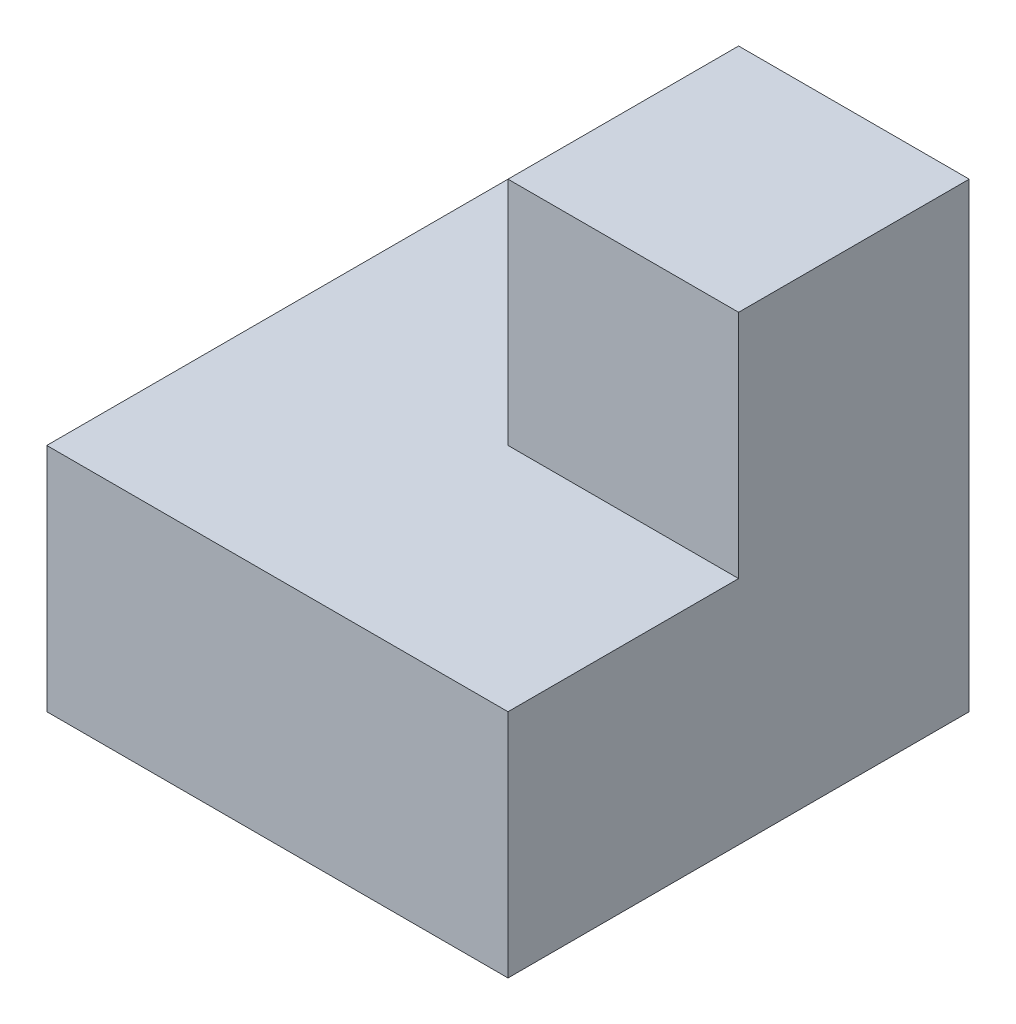
SolidWorks part; units mm, degrees
ref_plane "Front" through (0, 0, 0) normal (0, 0, 1) x (1, 0, 0)
ref_plane "Top" through (0, 0, 0) normal (0, 1, 0) x (1, 0, 0)
ref_plane "Right" through (0, 0, 0) normal (1, 0, 0) x (0, 0, -1)
sketch "Sketch1" plane through (0, 0, 0) normal (0, 1, 0) x (1, 0, 0)
  line L1 (0, 0) -> (4, 0)
  line L2 (0, 0) -> (0, 4)
  line L3 (0, 4) -> (4, 4)
  line L4 (4, 0) -> (4, 4)
  dimension "D1" = 4
  dimension "D2" = 4
extrude "Boss-Extrude1" add sketch "Sketch1" along normal blind 4
sketch "Sketch2" plane through (0, 4, 0) normal (0, 1, 0) x (1, 0, 0)
  line L1 (4, 4) -> (2, 4)
  line L2 (4, 4) -> (4, 2)
  line L3 (4, 2) -> (2, 2)
  line L4 (2, 4) -> (2, 2)
  line M1 (0, 4) -> (0, 0)
  line M2 (0, 0) -> (4, 0)
  line M3 (4, 0) -> (4, 4)
  line M4 (4, 4) -> (0, 4)
  dimension "D1" = 2
  dimension "D2" = 2
extrude "Cut-Extrude1" cut sketch "Sketch2" against normal blind 2 contours L4 L3 M4 M1 M2 M3
